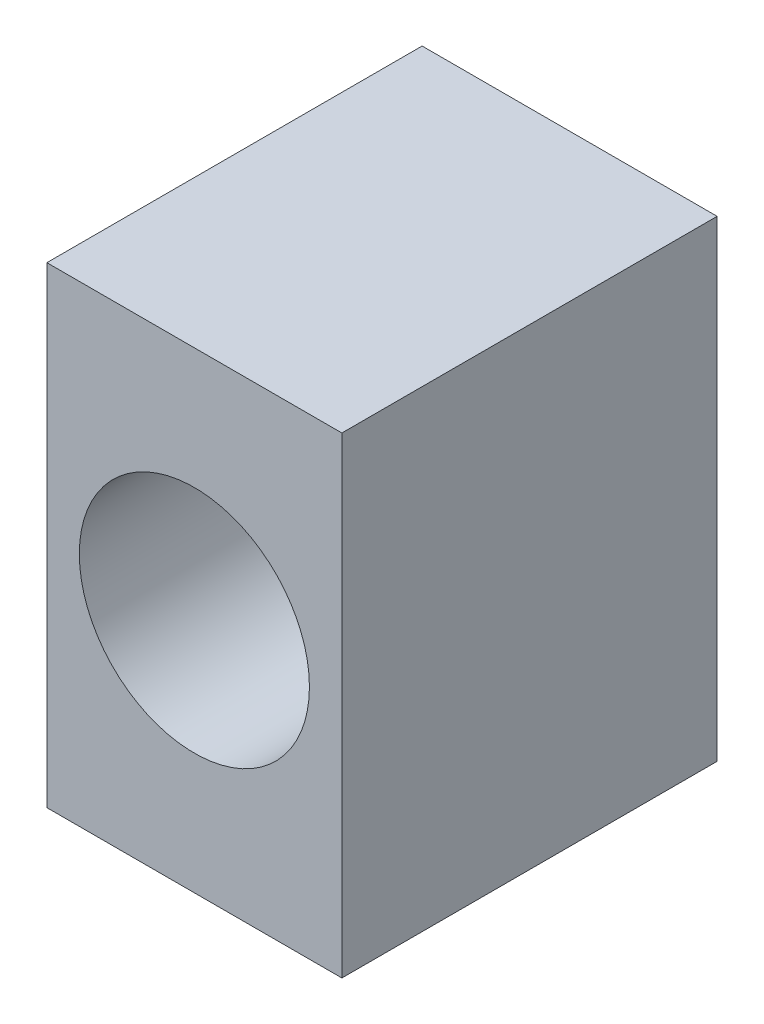
SolidWorks part; units mm, degrees
ref_plane "Front Plane" through (0, 0, 0) normal (0, 0, 1) x (1, 0, 0)
ref_plane "Top Plane" through (0, 0, 0) normal (0, 1, 0) x (1, 0, 0)
ref_plane "Right Plane" through (0, 0, 0) normal (1, 0, 0) x (0, 0, -1)
sketch "Sketch2" plane through (0, 0, 0) normal (0, 0, 1) x (1, 0, 0)
  line L5 (-1.25, 2) -> (1.25, 2)
  line L6 (-1.25, 2) -> (-1.25, -2)
  line L7 (-1.25, -2) -> (1.25, -2)
  line L8 (1.25, 2) -> (1.25, -2)
  line L9 (-1.25, 2) -> (1.25, -2) construction
  line L10 (-1.25, -2) -> (1.25, 2) construction
  point P0 (0, 0)
  dimension "D1" = 2.5
  dimension "D2" = 4
extrude "Boss-Extrude1" add sketch "Sketch2" along normal blind 3.18
sketch "Sketch3" plane through (0, 0, 3.18) normal (0, 0, 1) x (1, 0, 0)
  circle A2 centre (0, 0) radius 0.975
  dimension "D1" = 1.95
extrude "Cut-Extrude1" cut sketch "Sketch3" against normal through all
